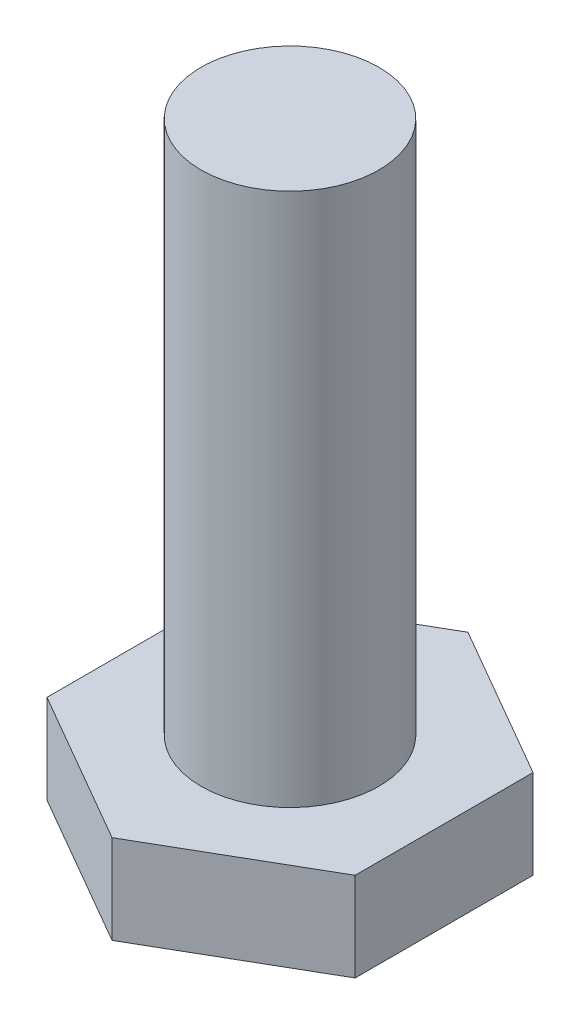
SolidWorks part; units mm, degrees
ref_plane "Front Plane" through (0, 0, 0) normal (0, 0, 1) x (1, 0, 0)
ref_plane "Top Plane" through (0, 0, 0) normal (0, 1, 0) x (1, 0, 0)
ref_plane "Right Plane" through (0, 0, 0) normal (1, 0, 0) x (0, 0, -1)
sketch "Sketch1" plane through (0, 0, 0) normal (0, 1, 0) x (1, 0, 0)
  circle A0 centre (0, 0) radius 1
  dimension "D1" = 2
extrude "Boss-Extrude1" add sketch "Sketch1" along normal blind 0.5
ref_plane "Plane1" through (0, 0.5, 0) normal (0, 1, 0) x (1, 0, 0)
sketch "Sketch2" plane through (0, 0.5, 0) normal (0, 1, 0) x (1, 0, 0)
  circle A0 centre (0, 0) radius 0.5
extrude "Boss-Extrude2" add sketch "Sketch2" along normal blind 3
ref_plane "Plane2" through (0, 0, 0) normal (0, -1, 0) x (-1, 0, 0)
sketch "Sketch3" plane through (0, 0, 0) normal (0, -1, 0) x (-1, 0, 0)
  line L0 (0, 0) -> (0, 1)
  line L1 (0, 1) -> (0.866, 0.5)
  line L2 (0.866, 0.5) -> (0, 0)
  line L3 (0.866, 0.5) -> (0.866, -0.5)
  line L4 (0.866, -0.5) -> (0, -1)
  line L5 (0, -1) -> (-0.866, -0.5)
  line L6 (-0.866, -0.5) -> (-0.866, 0.5)
  line L7 (-0.866, 0.5) -> (0, 1)
  circle A0 centre (0, 0) radius 1 construction
  point P19 (0, 0)
  dimension "D1" = 6
extrude "Cut-Extrude1" cut sketch "Sketch3" against normal blind 10 flip side to cut contours L2 L1 L0 | L7 L6 L5 L4 L3 L2 L0
